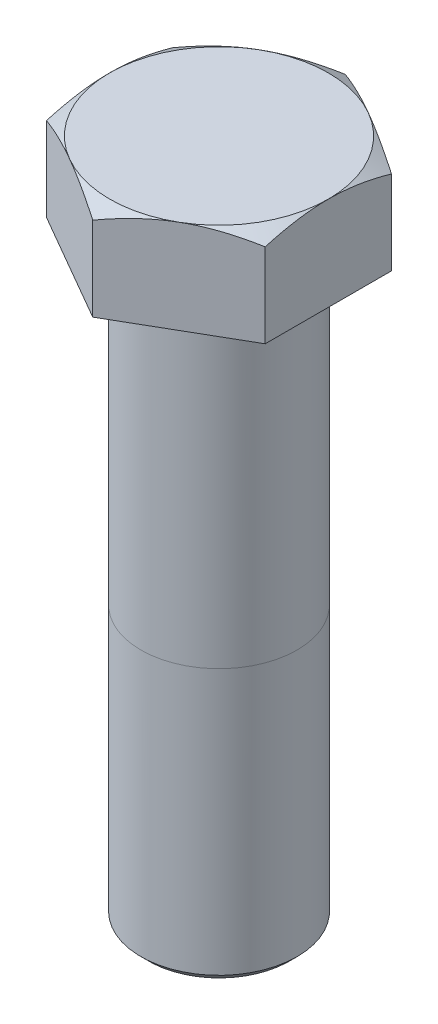
SolidWorks part; units mm, degrees
ref_plane "Front Plane" through (0, 0, 0) normal (0, 0, 1) x (1, 0, 0)
ref_plane "Top Plane" through (0, 0, 0) normal (0, 1, 0) x (1, 0, 0)
ref_plane "Right Plane" through (0, 0, 0) normal (1, 0, 0) x (0, 0, -1)
sketch "Sketch1" plane through (0, 0, 0) normal (0, 1, 0) x (1, 0, 0)
  line L1 (14, 8.0829) -> (0, 16.1658)
  line L2 (0, 16.1658) -> (-14, 8.0829)
  line L3 (-14, 8.0829) -> (-14, -8.0829)
  line L4 (-14, -8.0829) -> (0, -16.1658)
  line L5 (0, -16.1658) -> (14, -8.0829)
  line L6 (14, -8.0829) -> (14, 8.0829)
  circle A0 centre (0, 0) radius 14 construction
  dimension "D1" = 28
extrude "Boss-Extrude1" add sketch "Sketch1" along normal blind 12
sketch "Sketch2" plane through (0, 12, 0) normal (0, 1, 0) x (1, 0, 0)
  line L0 (14, 8.0829) -> (0, 16.1658) construction
  circle A0 centre (0, 0) radius 14
extrude "Cut-Extrude1" cut sketch "Sketch2" against normal blind 12 draft 60 flip side to cut
sketch "Sketch3" plane through (0, 0, 0) normal (0, -1, 0) x (1, 0, 0)
  circle A0 centre (0, 0) radius 10
  dimension "D1" = 20
extrude "Boss-Extrude2" add sketch "Sketch3" along normal blind 75
chamfer "Chamfer1" distance 1 angle 45 1 edges at (0, -75, -10)
sketch "Sketch4" plane through (0, 0, 0) normal (0, 0, 1) x (1, 0, 0)
  line L0 (-10, -40) -> (10, -40)
  line L1 (-10, 0) -> (-10, -74) construction
  line L2 (10, -74) -> (10, 0) construction
  line L3 (-10, 0) -> (10, 0) construction
  dimension "D1" = 40
split line "Split Line1"
